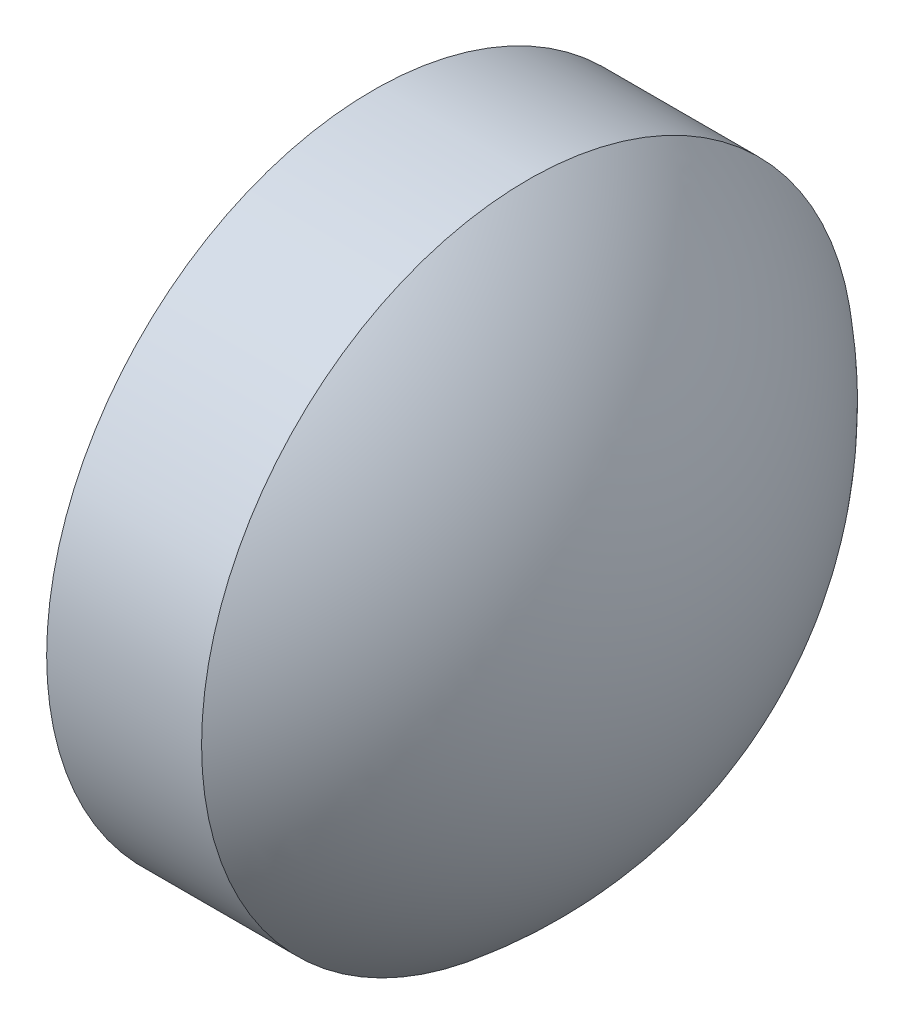
SolidWorks part; units mm, degrees
ref_plane "前视基准面" through (0, 0, 0) normal (0, 0, 1) x (1, 0, 0)
ref_plane "上视基准面" through (0, 0, 0) normal (0, 1, 0) x (1, 0, 0)
ref_plane "右视基准面" through (0, 0, 0) normal (1, 0, 0) x (0, 0, -1)
sketch "草图1" plane through (0, 0, 0) normal (0, 0, 1) x (1, 0, 0)
  line L0 (385.3162, -62.7757) -> (388.0137, -62.7757) construction
  line L1 (385.7148, -62.7757) -> (385.7148, -60.7744)
  line L2 (385.7148, -60.7744) -> (386.6648, -60.7744)
  line L3 (387.6148, -62.7757) -> (385.7148, -62.7757)
  arc A0 (387.6148, -62.7757) -> (386.6648, -60.7744) centre (385.0345, -62.7744) ccw
  point P1 (385.7148, -62.7757)
revolve "旋转2" add sketch "草图1" angle 360 about L0
